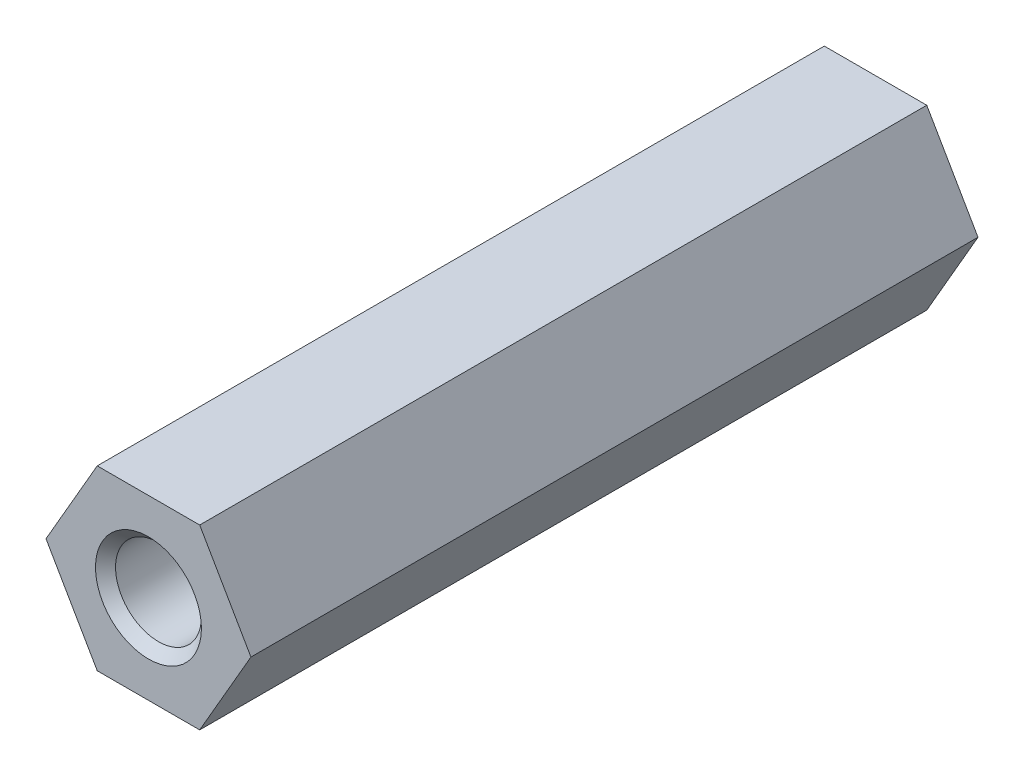
SolidWorks part; units mm, degrees
material "Alloy Steel"
ref_plane "Front Plane" through (0, 0, 0) normal (0, 0, 1) x (1, 0, 0)
ref_plane "Top Plane" through (0, 0, 0) normal (0, 1, 0) x (1, 0, 0)
ref_plane "Right Plane" through (0, 0, 0) normal (1, 0, 0) x (0, 0, -1)
ref_plane "Plane1" through (0, 0, 25.4) normal (0, 0, 1) x (1, 0, 0)
sketch "Sketch1" plane through (0, 0, 25.4) normal (0, 0, 1) x (1, 0, 0)
  line L0 (-3.5796, 0) -> (-1.7898, -3.1)
  line L1 (-1.7898, -3.1) -> (1.7898, -3.1)
  line L2 (1.7898, -3.1) -> (3.5796, 0)
  line L3 (3.5796, 0) -> (1.7898, 3.1)
  line L4 (1.7898, 3.1) -> (-1.7898, 3.1)
  line L5 (-1.7898, 3.1) -> (-3.5796, 0)
extrude "Boss-Extrude1" add sketch "Sketch1" against normal blind 25.4
hole_wizard "Ø3.0 (3) Diameter Hole1" positions "Sketch3" profile "Sketch2" hole size "Ø3.0" standard "ANSI Metric"
sketch "Sketch3" plane through (0, 0, 25.4) normal (0, 0, 1) x (1, 0, 0)
  point P0 (0, 0)
sketch "Sketch2" plane through (0, 0, 25.4) normal (1, 0, 0) x (0, -1, 0)
  line L0 (0, 0) -> (0, 25.4)
  line L1 (0, 25.4) -> (1.5, 25.4)
  line L2 (1.5, 25.4) -> (1.5, 0)
  line L5 (1.5, 0) -> (0, 0)
  line L11 (0, -6.35) -> (0, 107.95) construction
  dimension "Thru Hole Dia." = 3
  dimension "Thru Hole Depth" = 25.4
chamfer "Chamfer1" distance 0.35 angle 45 2 edges at (1.5, 0, 0) (1.5, 0, 25.4)
